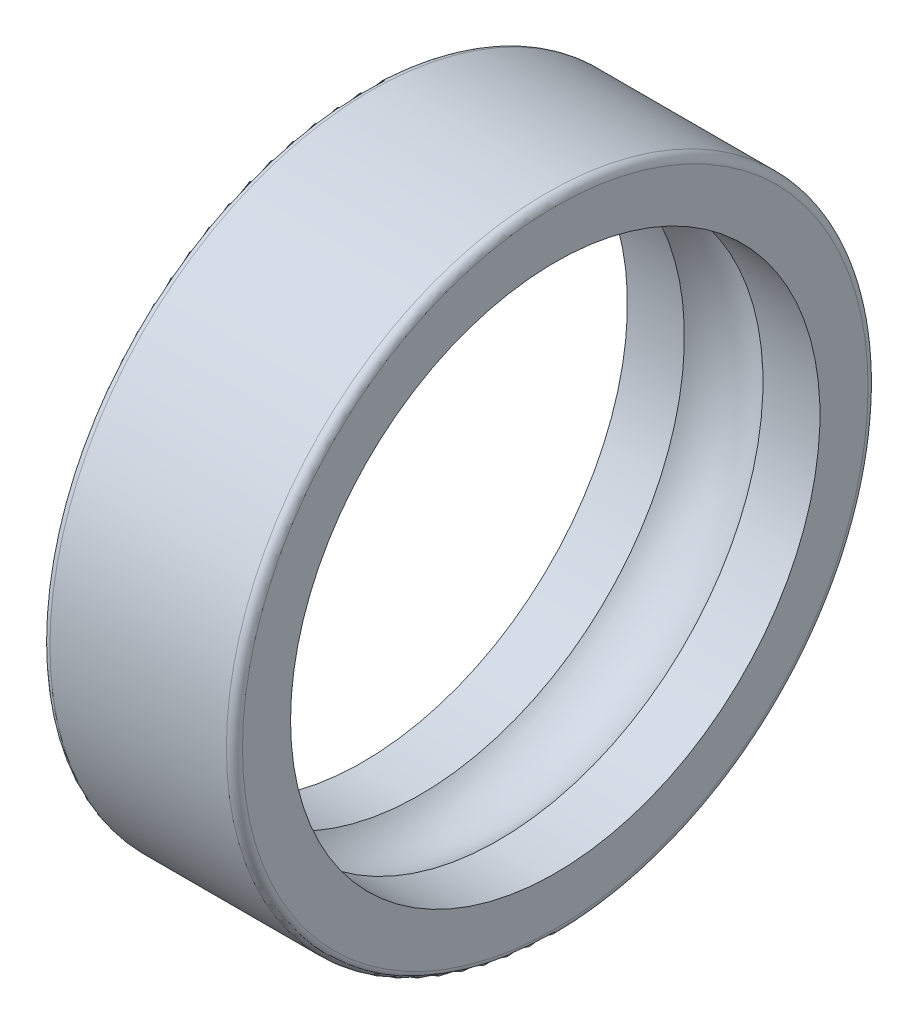
SolidWorks part; units mm, degrees
ref_plane "Front Plane" through (0, 0, 0) normal (0, 0, 1) x (1, 0, 0)
ref_plane "Top Plane" through (0, 0, 0) normal (0, 1, 0) x (1, 0, 0)
ref_plane "Right Plane" through (0, 0, 0) normal (1, 0, 0) x (0, 0, -1)
sketch "Sketch1" plane through (0, 0, 0) normal (0, 0, 1) x (1, 0, 0)
  line L0 (-10.5376, -14) -> (20.8737, -14) construction
  line L1 (-0.8319, 2.5) -> (-0.8319, 5.5)
  line L2 (-0.3319, 6) -> (10.6681, 6)
  line L3 (11.1681, 5.5) -> (11.1681, 2.5)
  line L4 (11.1681, 2.5) -> (7.6176, 2.5)
  line L5 (2.7186, 2.5) -> (-0.8319, 2.5)
  arc A2 (-0.8319, 5.5) -> (-0.3319, 6) centre (-0.3319, 5.5) cw
  arc A3 (10.6681, 6) -> (11.1681, 5.5) centre (10.6681, 5.5) cw
  arc A4 (7.6176, 2.5) -> (2.7186, 2.5) centre (5.1681, 0) ccw
  point P4 (0, 0)
  point P12 (-0.8319, 6)
  point P15 (11.1681, 6)
  point P17 (5.1681, -14)
  dimension "D2" = 3.5
  dimension "D5" = 0.5
  dimension "D1" = 12
  dimension "D3" = 20
revolve "Revolve1" add sketch "Sketch1" angle 360 about L0
